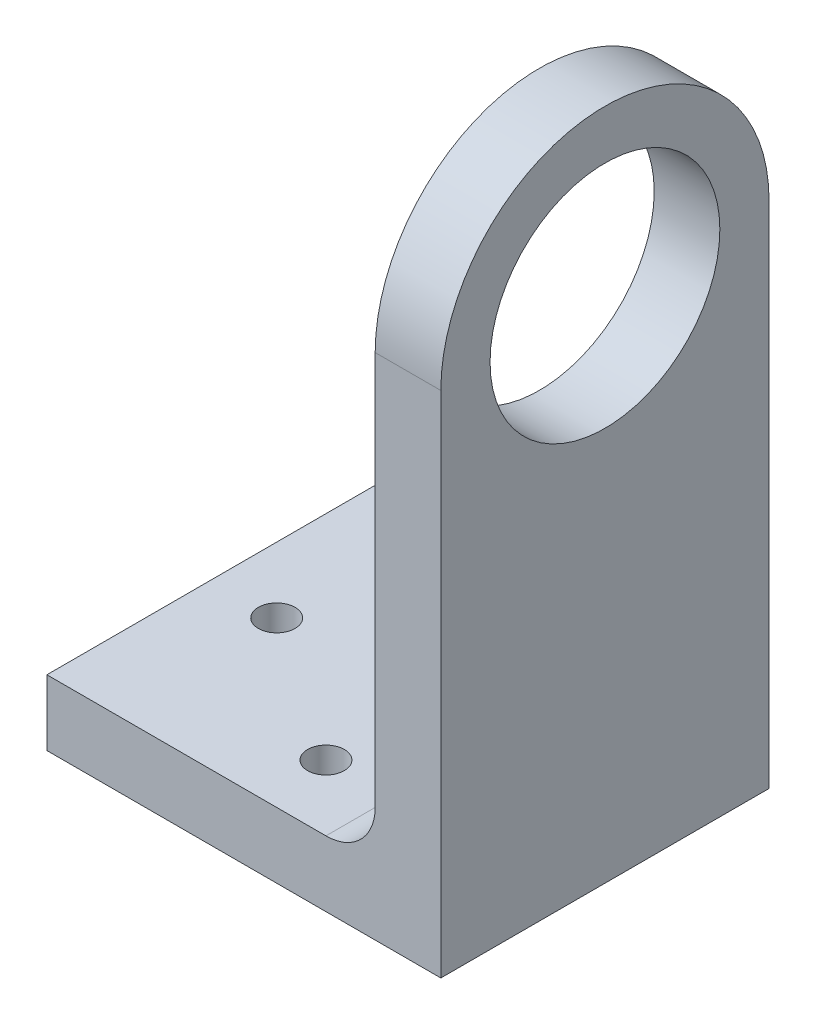
SolidWorks part; units mm, degrees
ref_plane "Front Plane" through (0, 0, 0) normal (0, 0, 1) x (1, 0, 0)
ref_plane "Top Plane" through (0, 0, 0) normal (0, 1, 0) x (1, 0, 0)
ref_plane "Right Plane" through (0, 0, 0) normal (1, 0, 0) x (0, 0, -1)
sketch "Sketch3" plane through (0, 0, 0) normal (1, 0, 0) x (0, 0, -1)
  line L1 (0, 0) -> (31.75, 0)
  line L2 (0, 0) -> (0, 42.8625)
  line L4 (31.75, 0) -> (31.75, 42.8625)
  circle A4 centre (15.875, 42.8625) radius 11.1125
  arc A5 (0, 42.8625) -> (31.75, 42.8625) centre (15.875, 42.8625) cw
  point P34 (15.875, 0)
  dimension "D4" = 22.225
  dimension "D1" = 42.8625
  dimension "D2" = 31.75
extrude "Boss-Extrude1" add sketch "Sketch3" along normal blind 6.35
sketch "Sketch5" plane through (6.35, 0, 0) normal (1, 0, 0) x (0, 0, -1)
  line L1 (0, 0) -> (31.75, 0)
  line L2 (0, 0) -> (0, -6.35)
  line L3 (0, -6.35) -> (31.75, -6.35)
  line L4 (31.75, 0) -> (31.75, -6.35)
  dimension "D1" = 6.35
extrude "Boss-Extrude2" add sketch "Sketch5" against normal blind 38.1
fillet "Fillet1" radius 4.7625 1 edges at (0, 0, -15.875)
sketch "Sketch6" plane through (0, 0, 0) normal (0, 1, 0) x (1, 0, 0)
  line L0 (-31.75, 0) -> (-4.7625, 0) construction
  line L1 (-4.7625, 0) -> (-4.7625, 31.75) construction
  line L2 (-31.75, 31.75) -> (-31.75, 0) construction
  line L3 (0, 15.875) -> (-33.0413, 15.875) construction
  line L4 (0, 31.75) -> (0, 0) construction
  circle A0 centre (-11.1125, 6.35) radius 1.777
  circle A2 centre (-25.4, 15.875) radius 1.777
  circle A3 centre (-11.1125, 25.4) radius 1.777
  dimension "D1" = 3.554
  dimension "D2" = 6.35
  dimension "D3" = 6.35
  dimension "D4" = 6.35
extrude "Cut-Extrude1" cut sketch "Sketch6" against normal through all
equation "\"D1@Sketch6\" = 3.3mm + \"normtol\""
equation "\"tighttol\" = 0.005in"
equation "\"normtol\" = 0.01in"
equation "\"loosetol\" = 0.02in"
equation "\"Fry height\"= 0.5in"
equation "\"Fry spacing\"= 0.5625in"
equation "\"Potato width\"= \"Fry spacing\" * 4"
equation "\"Potato length\"= 80mm"
equation "\"top robot surface separation\" = 0.6875"
equation "\"D1@Sketch3\"=1+\"top robot surface separation\""
